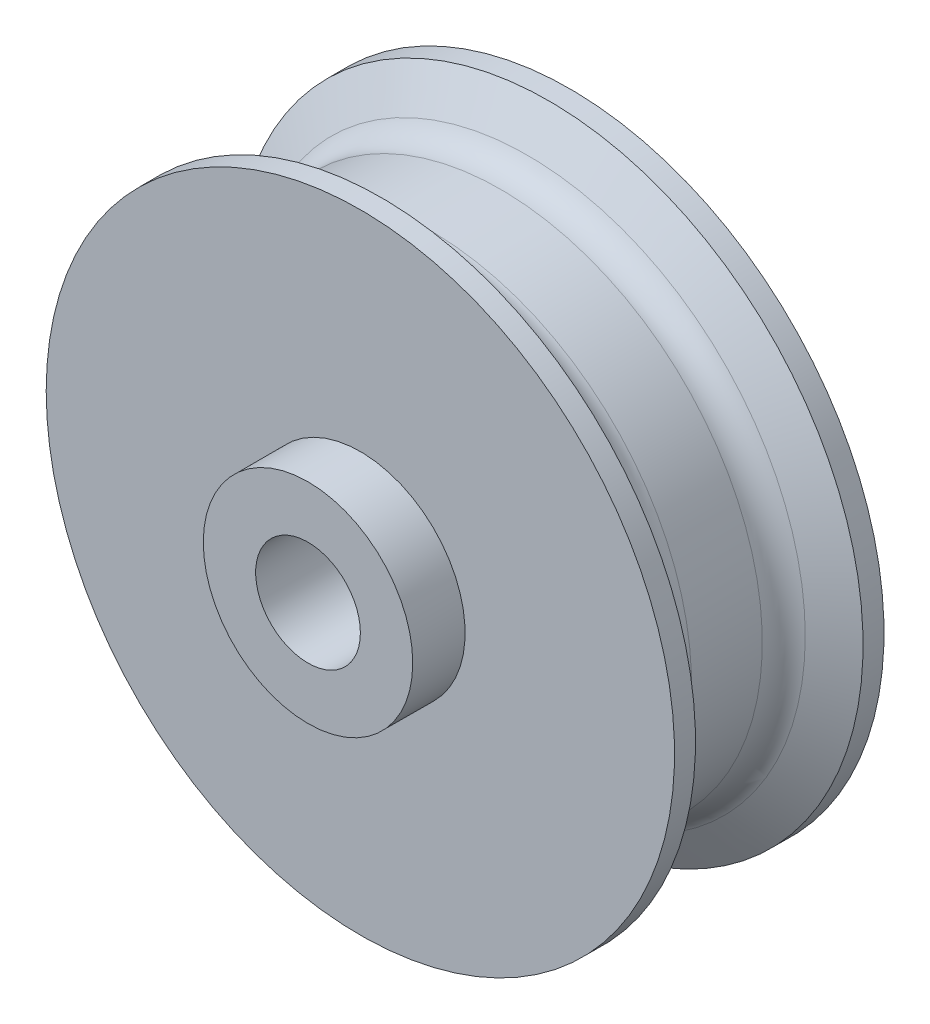
SolidWorks part; units mm, degrees
ref_plane "Front Plane" through (0, 0, 0) normal (0, 0, 1) x (1, 0, 0)
ref_plane "Top Plane" through (0, 0, 0) normal (0, 1, 0) x (1, 0, 0)
ref_plane "Right Plane" through (0, 0, 0) normal (1, 0, 0) x (0, 0, -1)
sketch "Sketch1" plane through (0, 0, 0) normal (0, 0, 1) x (1, 0, 0)
  circle A0 centre (0, 0) radius 5
  circle A1 centre (0, 0) radius 10
  dimension "D1" = 10
  dimension "D2" = 20
extrude "Boss-Extrude1" add sketch "Sketch1" along normal blind 30
sketch "Sketch4" plane through (0, 0, 0) normal (0, 1, 0) x (1, 0, 0)
  line L0 (10, 0) -> (10, -5)
  line L1 (10, -30) -> (10, 0) construction
  line L2 (10, -30) -> (10, -25)
  line L3 (10, -5) -> (30, -5)
  line L4 (10, -25) -> (30, -25)
  line L5 (30, -5) -> (30, -7)
  line L6 (25, -9.8868) -> (25, -20.1132)
  line L7 (30, -7) -> (25, -9.8868)
  line L8 (0, 0) -> (0, -30)
  line L9 (-10, -30) -> (10, -30) construction
  line L10 (10, -5) -> (10, -25)
  line L11 (30, -25) -> (30, -23)
  line L12 (30, -23) -> (25, -20.1132)
  dimension "D1" = 5
  dimension "D2" = 5
  dimension "D3" = 20
  dimension "D4" = 20
  dimension "D5" = 5
  dimension "D6" = 2
  dimension "D7" = 2
  dimension "D8" = 120
  dimension "D9" = 120
revolve "Revolve1" add sketch "Sketch4" angle 360 about L8
fillet "Fillet1" radius 3 2 edges at (-25, 0, 20.1132) (-25, 0, 9.8868)
